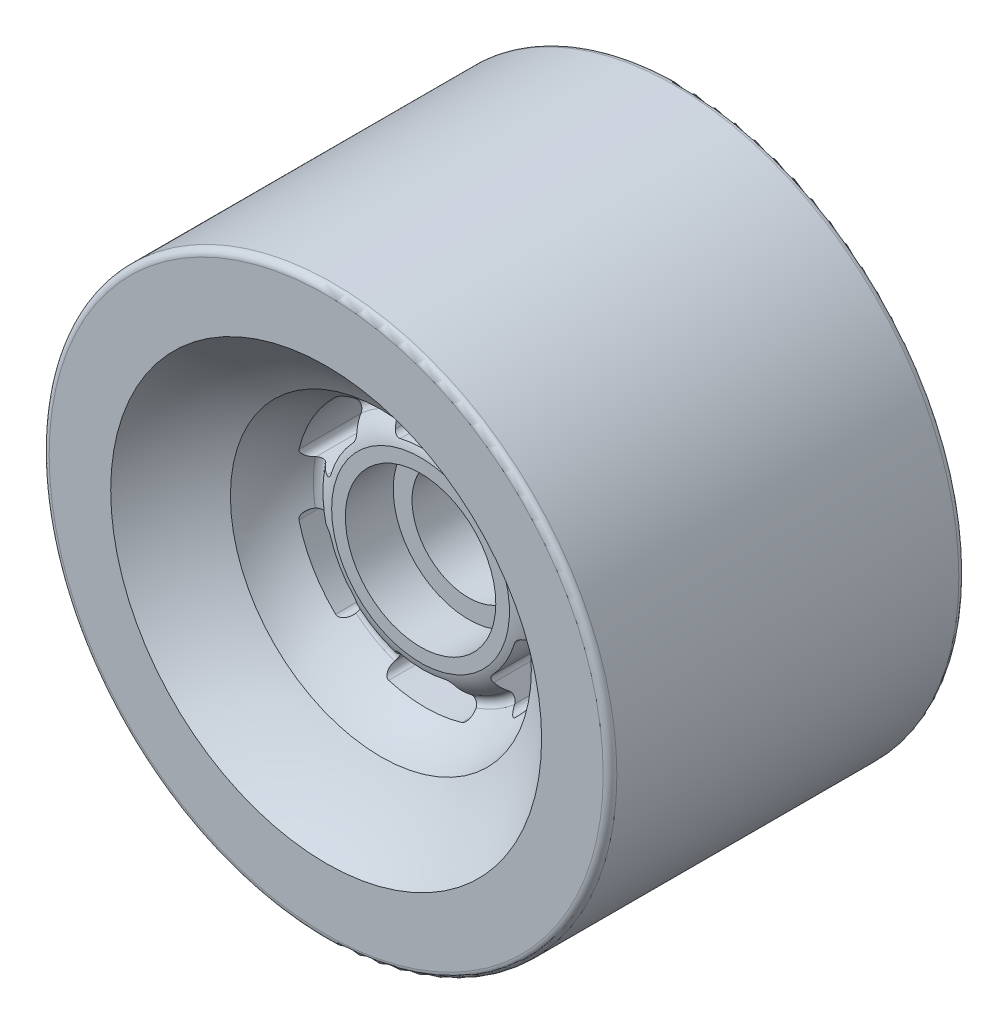
SolidWorks part; units mm, degrees
ref_plane "Front Plane" through (0, 0, 0) normal (0, 0, 1) x (1, 0, 0)
ref_plane "Top Plane" through (0, 0, 0) normal (0, 1, 0) x (1, 0, 0)
ref_plane "Right Plane" through (0, 0, 0) normal (1, 0, 0) x (0, 0, -1)
sketch "Sketch1" plane through (0, 0, 0) normal (0, 0, 1) x (1, 0, 0)
  circle A0 centre (0, 0) radius 41.5
  dimension "D1" = 83
extrude "Boss-Extrude1" add sketch "Sketch1" along normal mid plane 52
ref_plane "Plane1" through (0, 0, 12.2) normal (0, 0, 1) x (1, 0, 0)
ref_plane "Plane2" through (0, 0, -12.2) normal (0, 0, -1) x (-1, 0, 0)
sketch "Sketch3" plane through (0, 0, 12.2) normal (0, 0, 1) x (1, 0, 0)
  circle A0 centre (0, 0) radius 11
  dimension "D1" = 22
ref_plane "Plane3" through (0, 0, 18) normal (0, 0, 1) x (1, 0, 0)
ref_plane "Plane4" through (0, 0, -18) normal (0, 0, -1) x (-1, 0, 0)
sketch "Sketch4" plane through (0, 0, 26) normal (0, 0, 1) x (1, 0, 0)
  circle A0 centre (0, 0) radius 31.5
  circle A1 centre (0, 0) radius 41.5 construction
  dimension "D1" = 10
  dimension "D2" = 63
sketch "Sketch5" plane through (0, 0, 18) normal (0, 0, 1) x (1, 0, 0)
  circle A0 centre (0, 0) radius 22
  dimension "D1" = 44
sketch "Sketch7" plane through (0, 0, 0) normal (1, 0, 0) x (0, 0, -1)
  line L0 (-26, 31.5) -> (-26, -31.5) construction
  line L1 (-18, 22) -> (-18, -22) construction
  line L2 (-18, 22) -> (-18, 0)
  line L3 (-18, 0) -> (-26, 0)
  line L4 (-26, 0) -> (-26, 31.5)
  arc A0 (-26, 31.5) -> (-18, 22) centre (-47.6215, 5.174) cw
  dimension "D1" = 22
  dimension "D2" = 31.5
revolve "Cut-Revolve1" cut sketch "Sketch7" angle 360 about axis through (0, 0, 26) along (0, 0, -1)
sketch "Sketch8" plane through (0, 0, 0) normal (1, 0, 0) x (0, 0, -1)
  line L0 (-18, 22) -> (-18, -22) construction
  line L1 (-12.2, 11) -> (-12.2, -11) construction
  line L2 (-12.2, 13) -> (-12.2, 0)
  line L3 (-12.2, 0) -> (-18, 0)
  line L4 (-18, 0) -> (-18, 22)
  arc A0 (-18, 22) -> (-10.0425, 17.8422) centre (-22.6655, 3.3772) cw
  arc A1 (-12.2, 13) -> (-10.1037, 16.286) centre (-6.8393, 11.8918) cw
  arc A2 (-10.0425, 17.8422) -> (-10.1037, 16.286) centre (-10.7, 17.0887) cw
  dimension "D1" = 1
  dimension "D2" = 1.5
  dimension "D3" = 13
  dimension "D4" = 22
sketch "Sketch9" plane through (0, 0, 18) normal (0, 0, 1) x (1, 0, 0)
  line L0 (0, -19.7649) -> (0, 57.7649) construction
  line L1 (4.3781, 14.0831) -> (5.931, 16.7727)
  line L2 (-4.3781, 14.0831) -> (-5.931, 16.7727)
  line L3 (10.0072, 10.8331) -> (11.5601, 13.5227)
  line L4 (14.3853, 3.25) -> (17.4911, 3.25)
  line L5 (14.3853, -3.25) -> (17.4911, -3.25)
  line L6 (10.0072, -10.8331) -> (11.5601, -13.5227)
  line L7 (4.3781, -14.0831) -> (5.931, -16.7727)
  line L8 (-4.3781, -14.0831) -> (-5.931, -16.7727)
  line L9 (-10.0072, -10.8331) -> (-11.5601, -13.5227)
  line L10 (-14.3853, -3.25) -> (-17.4911, -3.25)
  line L11 (-14.3853, 3.25) -> (-17.4911, 3.25)
  line L12 (-10.0072, 10.8331) -> (-11.5601, 13.5227)
  arc A0 (-5.3463, 18.2323) -> (5.3463, 18.2323) centre (0, 0) cw
  arc A1 (-3.2779, 13.6109) -> (3.2779, 13.6109) centre (0, 0) cw
  circle A2 centre (0, 0) radius 11 construction
  circle A3 centre (0, 0) radius 22 construction
  arc A4 (3.2779, 13.6109) -> (4.3781, 14.0831) centre (3.5121, 14.5831) ccw
  arc A5 (5.3463, 18.2323) -> (5.931, 16.7727) centre (5.0649, 17.2727) cw
  arc A6 (-3.2779, 13.6109) -> (-4.3781, 14.0831) centre (-3.5121, 14.5831) cw
  arc A7 (-5.3463, 18.2323) -> (-5.931, 16.7727) centre (-5.0649, 17.2727) ccw
  arc A8 (13.1165, 13.7462) -> (11.5601, 13.5227) centre (12.4261, 13.0227) ccw
  arc A9 (10.1484, 9.6442) -> (10.0072, 10.8331) centre (10.8733, 10.3331) cw
  arc A10 (13.1165, 13.7462) -> (18.4628, 4.4861) centre (0, 0) cw
  arc A11 (18.4628, 4.4861) -> (17.4911, 3.25) centre (17.4911, 4.25) cw
  arc A12 (13.4263, 3.9667) -> (14.3853, 3.25) centre (14.3853, 4.25) ccw
  arc A13 (10.1484, 9.6442) -> (13.4263, 3.9667) centre (0, 0) cw
  arc A14 (18.4628, -4.4861) -> (17.4911, -3.25) centre (17.4911, -4.25) ccw
  arc A15 (13.4263, -3.9667) -> (14.3853, -3.25) centre (14.3853, -4.25) cw
  arc A16 (18.4628, -4.4861) -> (13.1165, -13.7462) centre (0, 0) cw
  arc A17 (13.1165, -13.7462) -> (11.5601, -13.5227) centre (12.4261, -13.0227) cw
  arc A18 (10.1484, -9.6442) -> (10.0072, -10.8331) centre (10.8733, -10.3331) ccw
  arc A19 (13.4263, -3.9667) -> (10.1484, -9.6442) centre (0, 0) cw
  arc A20 (5.3463, -18.2323) -> (5.931, -16.7727) centre (5.0649, -17.2727) ccw
  arc A21 (3.2779, -13.6109) -> (4.3781, -14.0831) centre (3.5121, -14.5831) cw
  arc A22 (5.3463, -18.2323) -> (-5.3463, -18.2323) centre (0, 0) cw
  arc A23 (-5.3463, -18.2323) -> (-5.931, -16.7727) centre (-5.0649, -17.2727) cw
  arc A24 (-3.2779, -13.6109) -> (-4.3781, -14.0831) centre (-3.5121, -14.5831) ccw
  arc A25 (3.2779, -13.6109) -> (-3.2779, -13.6109) centre (0, 0) cw
  arc A26 (-13.1165, -13.7462) -> (-11.5601, -13.5227) centre (-12.4261, -13.0227) ccw
  arc A27 (-10.1484, -9.6442) -> (-10.0072, -10.8331) centre (-10.8733, -10.3331) cw
  arc A28 (-13.1165, -13.7462) -> (-18.4628, -4.4861) centre (0, 0) cw
  arc A29 (-18.4628, -4.4861) -> (-17.4911, -3.25) centre (-17.4911, -4.25) cw
  arc A30 (-13.4263, -3.9667) -> (-14.3853, -3.25) centre (-14.3853, -4.25) ccw
  arc A31 (-10.1484, -9.6442) -> (-13.4263, -3.9667) centre (0, 0) cw
  arc A32 (-18.4628, 4.4861) -> (-17.4911, 3.25) centre (-17.4911, 4.25) ccw
  arc A33 (-13.4263, 3.9667) -> (-14.3853, 3.25) centre (-14.3853, 4.25) cw
  arc A34 (-18.4628, 4.4861) -> (-13.1165, 13.7462) centre (0, 0) cw
  arc A35 (-13.1165, 13.7462) -> (-11.5601, 13.5227) centre (-12.4261, 13.0227) cw
  arc A36 (-10.1484, 9.6442) -> (-10.0072, 10.8331) centre (-10.8733, 10.3331) ccw
  arc A37 (-13.4263, 3.9667) -> (-10.1484, 9.6442) centre (0, 0) cw
  point P8 (0, 19)
  point P9 (0, 14)
  point P85 (0, 0)
  dimension "D2" = 3
  dimension "D3" = 3
  dimension "D4" = 1
  dimension "D1" = 6.5
  dimension "D5" = 6
extrude "Cut-Extrude1" cut sketch "Sketch9" along direction (0, 0, 1) on the side against the normal through all
revolve "Cut-Revolve2" cut sketch "Sketch8" angle 360
extrude "Cut-Extrude2" cut sketch "Sketch3" against normal blind 7 contours A0
sketch "Sketch10" plane through (0, 0, 5.2) normal (0, 0, 1) x (1, 0, 0)
  circle A0 centre (0, 0) radius 8.25
  dimension "D1" = 16.5
extrude "Cut-Extrude3" cut sketch "Sketch10" against normal through all
mirror "Mirror1" about plane through (0, 0, 0) normal (0, 0, 1) of "Cut-Revolve2", "Cut-Extrude2"
mirror "Mirror2" about plane through (0, 0, 0) normal (0, 0, 1) of "Cut-Revolve1"
fillet "Fillet1" radius 1 2 edges at (41.5, 0, -26) (41.5, 0, 26)
